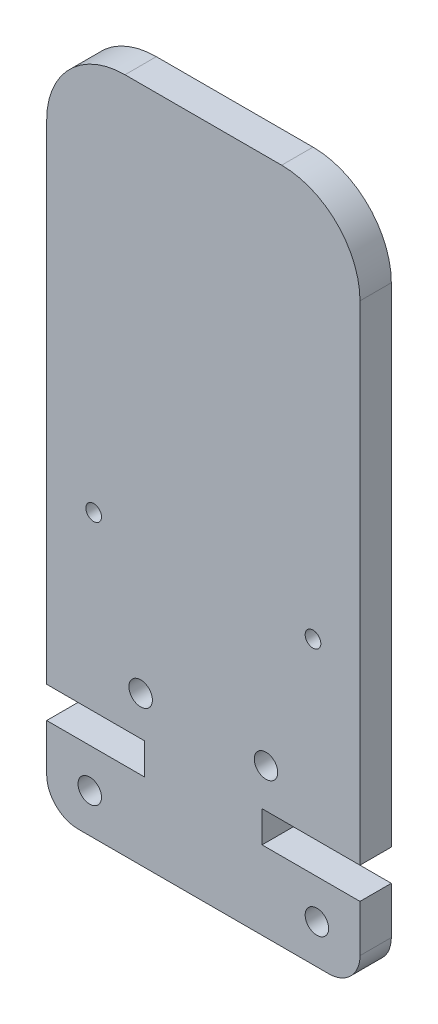
SolidWorks part; units mm, degrees
material "Acrylic (Medium-high impact)"
ref_plane "Front Plane" through (0, 0, 0) normal (0, 0, 1) x (1, 0, 0)
ref_plane "Top Plane" through (0, 0, 0) normal (0, 1, 0) x (1, 0, 0)
ref_plane "Right Plane" through (0, 0, 0) normal (1, 0, 0) x (0, 0, -1)
sketch "Model" plane through (0, 0, 0) normal (0, 0, 1) x (1, 0, 0)
  line L8 (2, 0) -> (18, 0)
  line L9 (5, 43.2) -> (15, 43.2)
  line L10 (0, 5) -> (0, 2)
  line L11 (20, 5) -> (20, 2)
  line L13 (6.25, 5) -> (0, 5)
  line L14 (13.75, 5) -> (20, 5)
  line L15 (6.25, 5) -> (6.25, 7)
  line L16 (6.25, 7) -> (0, 7)
  line L17 (13.75, 5) -> (13.75, 7)
  line L18 (13.75, 7) -> (20, 7)
  line L51 (20, 7) -> (20, 38.2)
  line L53 (0, 38.2) -> (0, 7)
  arc A10 (18, 0) -> (20, 2) centre (18, 2) ccw
  arc A11 (0, 2) -> (2, 0) centre (2, 2) ccw
  arc A12 (5, 43.2) -> (0, 38.2) centre (5, 38.2) ccw
  arc A13 (20, 38.2) -> (15, 43.2) centre (15, 38.2) ccw
  circle A14 centre (3, 18) radius 0.5
  circle A15 centre (17, 18) radius 0.5
  circle A19 centre (14, 9.5) radius 0.75
  circle A20 centre (6, 9.5) radius 0.75
  circle A65 centre (17.25, 2.5) radius 0.75
  circle A66 centre (2.75, 2.5) radius 0.75
  dimension "D1" = 1
  dimension "D2" = 1.5
  dimension "D3" = 2
  dimension "D4" = 5
  dimension "D5" = 20
  dimension "D6" = 2.75
  dimension "D7" = 0.25
  dimension "D8" = 3
  dimension "D9" = 0.25
  dimension "D10" = 0.25
  dimension "D11" = 43.2
  dimension "D12" = 3
  dimension "D13" = 0.25
  dimension "D14" = 2.5
  dimension "D15" = 2.5
  dimension "D16" = 2
  dimension "D17" = 2.5
  dimension "D18" = 8.5
other "AlignGroup1"
other "AlignGroup2"
other "AlignGroup3"
extrude "Boss-Extrude1" add sketch "Model" along normal blind 2
